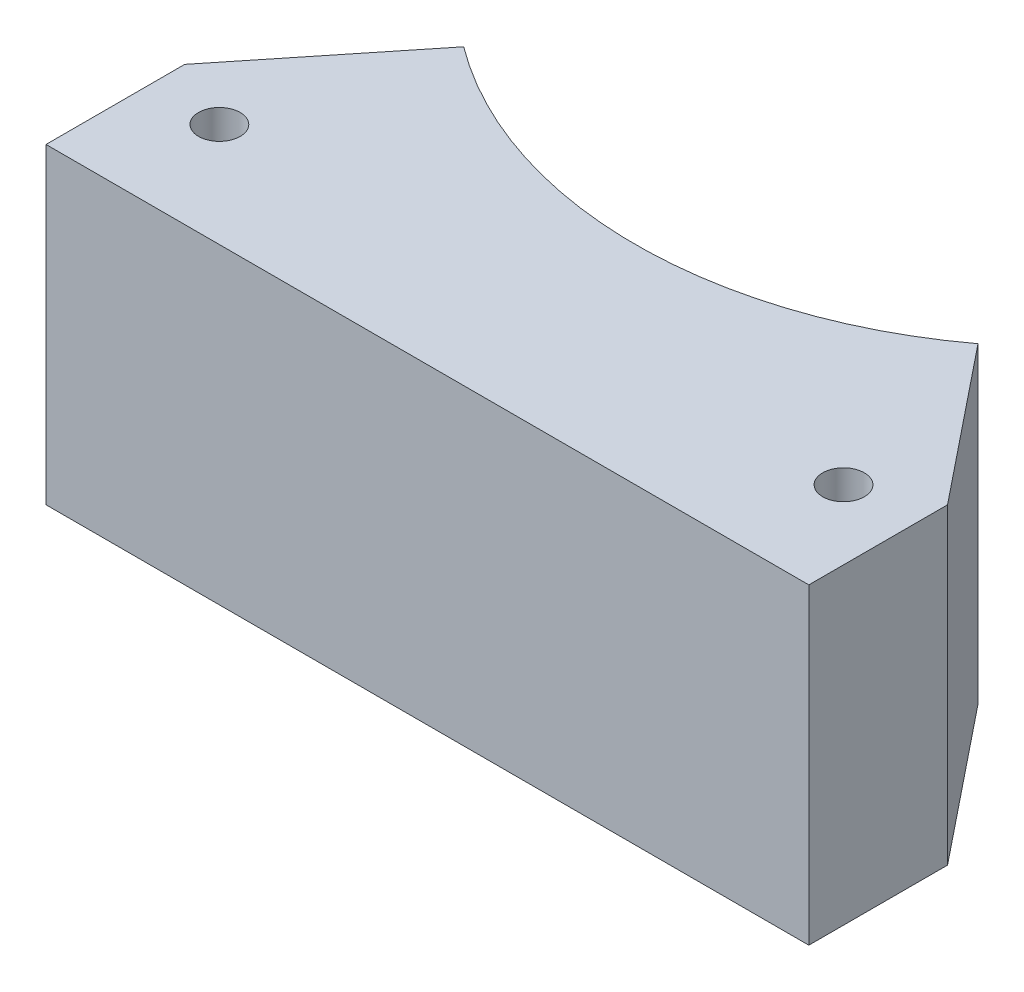
SolidWorks part; units mm, degrees
ref_plane "Front Plane" through (0, 0, 0) normal (0, 0, 1) x (1, 0, 0)
ref_plane "Top Plane" through (0, 0, 0) normal (0, 1, 0) x (1, 0, 0)
ref_plane "Right Plane" through (0, 0, 0) normal (1, 0, 0) x (0, 0, -1)
sketch "Sketch1" plane through (0, 0, 0) normal (0, 1, 0) x (1, 0, 0)
  line L0 (-33.134, -22.1634) -> (76.866, -22.1634)
  line L1 (76.866, -22.1634) -> (76.866, -2.1634)
  line L2 (-33.134, -2.1634) -> (76.866, -2.1634) construction
  line L3 (21.866, 69.8366) -> (21.866, 7.8366) construction
  line L4 (-33.134, -2.1634) -> (-33.134, -22.1634)
  line L6 (-18.6567, 22.9121) -> (-33.134, -2.1634)
  line L7 (62.3887, 22.9121) -> (76.866, -2.1634)
  arc A0 (-18.6567, 22.9121) -> (62.3887, 22.9121) centre (21.866, 69.8366) ccw
  dimension "D3" = 60
  dimension "D4" = 124
  dimension "D5" = 30
  dimension "D1" = 110
  dimension "D2" = 20
  dimension "D6" = 60
  dimension "D7" = 81.626
extrude "Boss-Extrude1" add sketch "Sketch1" along normal blind 45
sketch "Sketch2" plane through (0, 45, 0) normal (0, 1, 0) x (1, 0, 0)
  line L0 (-33.134, -22.1634) -> (76.866, -22.1634) construction
  line L2 (76.866, -22.1634) -> (76.866, -2.1634) construction
  line L3 (-33.134, -2.1634) -> (-33.134, -22.1634) construction
  circle A0 centre (-23.134, -7.1634) radius 3
  circle A1 centre (66.866, -7.1634) radius 3
  dimension "D4" = 90
  dimension "D1" = 10
  dimension "D2" = 15
  dimension "D3" = 10
extrude "Cut-Extrude1" cut sketch "Sketch2" against normal through all
sketch "Sketch3" plane through (0, 0, 0) normal (0, -1, 0) x (1, 0, 0)
  line L0 (-12.0825, -24.0491) -> (-33.134, 2.1634)
  line L2 (-33.134, 2.1634) -> (-36.1142, -37.1462)
  line L3 (-36.1142, -37.1462) -> (-12.0825, -24.0491)
  line L4 (21.866, 22.1634) -> (21.866, -18.6698) construction
  line L5 (-33.134, 22.1634) -> (76.866, 22.1634) construction
  line L6 (79.8462, -37.1462) -> (55.8145, -24.0491)
  line L7 (76.866, 2.1634) -> (79.8462, -37.1462)
  line L8 (55.8145, -24.0491) -> (76.866, 2.1634)
extrude "Cut-Extrude3" cut sketch "Sketch3" against normal through all
